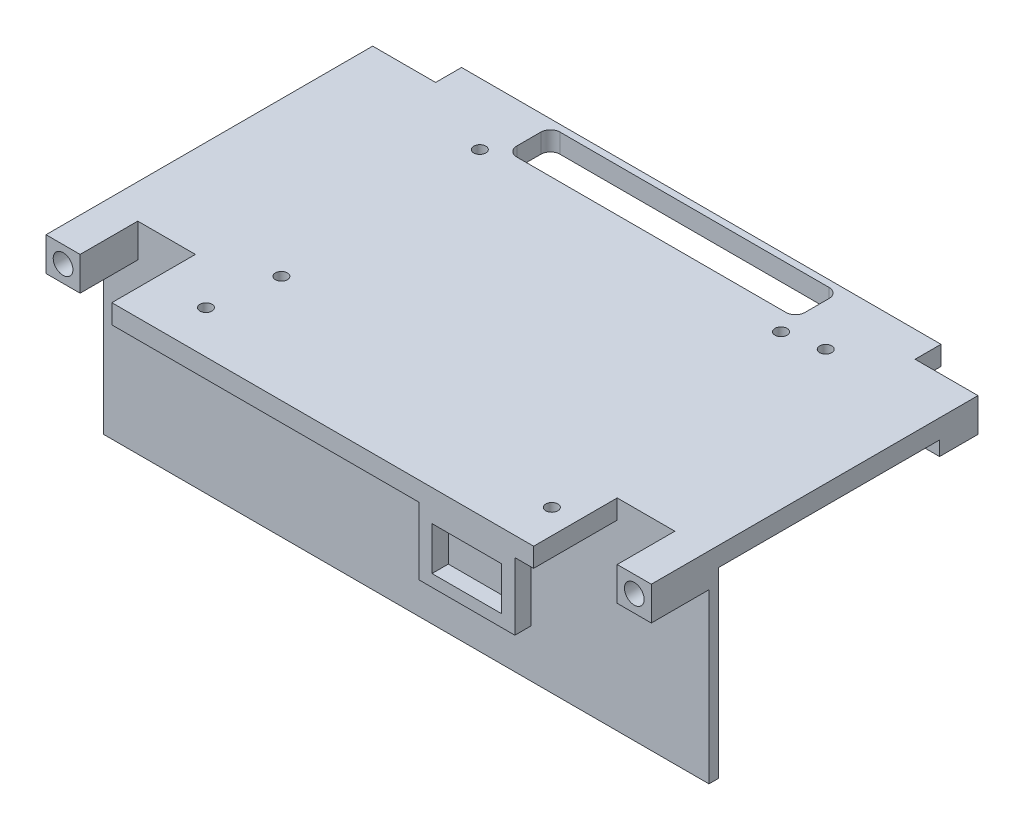
SolidWorks part; units mm, degrees
ref_plane "Front Plane" through (0, 0, 0) normal (0, 0, 1) x (1, 0, 0)
ref_plane "Top Plane" through (0, 0, 0) normal (0, 1, 0) x (1, 0, 0)
ref_plane "Right Plane" through (0, 0, 0) normal (1, 0, 0) x (0, 0, -1)
sketch "Sketch1" plane through (0, 0, 0) normal (0, 1, 0) x (1, 0, 0)
  line L0 (-63, 0) -> (63, 0) construction
  line L1 (-63, -34) -> (-55.9, -34)
  line L2 (-63, -34) -> (-63, 34)
  line L3 (-63, 34) -> (-55.9, 34)
  line L4 (63, -34) -> (63, 34)
  line L5 (-63, -34) -> (63, 34) construction
  line L6 (-63, 34) -> (63, -34) construction
  line L8 (-55.9, 34) -> (-55.9, 41)
  line L9 (-55.9, 41) -> (55.9, 41)
  line L10 (55.9, 34) -> (55.9, 41)
  line L11 (55.9, 34) -> (63, 34)
  line L12 (55.9, -34) -> (55.9, -41)
  line L13 (-55.9, -41) -> (55.9, -41)
  line L14 (-55.9, -34) -> (-55.9, -41)
  line L15 (55.9, -34) -> (63, -34)
  point P0 (0, 0)
  point P10 (0, 41)
  dimension "D1" = 126
  dimension "D2" = 68
  dimension "D3" = 7.1
  dimension "D4" = 7
extrude "Boss-Extrude1" add sketch "Sketch1" along normal blind 4
sketch "Sketch3" plane through (0, 0, 0) normal (0, -1, 0) x (1, 0, 0)
  line L0 (-63, -34) -> (-63, 34) construction
  line L1 (-55.9, -34) -> (-63, -34)
  line L2 (-55.9, -34) -> (-55.9, -26)
  line L3 (-55.9, -26) -> (-63, -26)
  line L4 (-63, -34) -> (-63, -26)
  dimension "D1" = 8
extrude "Boss-Extrude3" add sketch "Sketch3" along normal blind 3
sketch "Sketch4" plane through (0, 0, -34) normal (0, 0, -1) x (-1, 0, 0)
  line L0 (63, -3) -> (55.9, 4) construction
  circle A0 centre (59.45, 0.5) radius 2.05
  dimension "D1" = 4.1
extrude "Cut-Extrude1" cut sketch "Sketch4" against normal blind 7
mirror "Mirror1" about plane through (0, 0, 0) normal (1, 0, 0) of "Cut-Extrude1", "Boss-Extrude3"
mirror "Mirror2" about plane through (0, 0, 0) normal (0, 0, 1) of "Cut-Extrude1", "Boss-Extrude3", "Mirror1"
sketch "Sketch5" plane through (0, 4, 0) normal (0, 1, 0) x (1, 0, 0)
  line L0 (55.9, 41) -> (-55.9, 41) construction
  line L1 (-30, 38) -> (30, 38)
  line L2 (-30, 38) -> (-30, 29)
  line L3 (-30, 29) -> (30, 29)
  line L4 (30, 38) -> (30, 29)
  point P4 (0, 29)
  dimension "D1" = 3
  dimension "D2" = 9
  dimension "D3" = 60
extrude "Cut-Extrude2" cut sketch "Sketch5" against normal through all
sketch "Sketch6" plane through (0, 4, 0) normal (0, 1, 0) x (1, 0, 0)
  line L1 (-38.5, -28) -> (38.5, -28) construction
  line L2 (-38.5, -28) -> (-38.5, 24) construction
  line L3 (-38.5, 24) -> (38.5, 24) construction
  line L4 (38.5, -28) -> (38.5, 24) construction
  line L5 (-38.5, -28) -> (38.5, 24) construction
  line L6 (-38.5, 24) -> (38.5, -28) construction
  circle A0 centre (-38.5, 24) radius 1.25
  circle A1 centre (38.5, 24) radius 1.25
  circle A2 centre (38.5, -28) radius 1.25
  circle A3 centre (-38.5, -28) radius 1.25
  point P0 (0, -2)
  point P9 (0, -2)
  dimension "D4" = 2.5
  dimension "D1" = 77
  dimension "D2" = 52
  dimension "D3" = 2
fillet "Fillet1" radius 2 4 edges at (-30, 2, -38) (-30, 2, -29) (30, 2, -38) (30, 2, -29)
sketch "Sketch7" plane through (0, 4, 0) normal (0, 1, 0) x (1, 0, 0)
  line L0 (55.9, 34) -> (55.9, 41) construction
  line L1 (-55.9, 41) -> (55.9, 41)
  line L2 (-55.9, 41) -> (-55.9, 40)
  line L3 (-55.9, 40) -> (55.9, 40)
  line L4 (55.9, 41) -> (55.9, 40)
  line L5 (-55.9, -34) -> (-55.9, -41) construction
  line L6 (55.9, -41) -> (-55.9, -41)
  line L7 (55.9, -41) -> (55.9, -40)
  line L8 (55.9, -40) -> (-55.9, -40)
  line L9 (-55.9, -41) -> (-55.9, -40)
  dimension "D1" = 1
  dimension "D2" = 1
extrude "Cut-Extrude3" cut sketch "Sketch7" against normal through all
sketch "Sketch8" plane through (0, 0, 0) normal (0, -1, 0) x (1, 0, 0)
  line L0 (63, 26) -> (63, -26) construction
  line L1 (63, 22) -> (-63, 22)
  line L2 (63, 22) -> (63, 20)
  line L3 (63, 20) -> (-63, 20)
  line L4 (-63, 22) -> (-63, 20)
  line L5 (-63, -26) -> (-63, 26) construction
  line L7 (55.9, 40) -> (-55.9, 40) construction
  dimension "D1" = 20
  dimension "D2" = 2
extrude "Boss-Extrude4" add sketch "Sketch8" along normal blind 38
sketch "Sketch9" plane through (0, 4, 0) normal (0, 1, 0) x (1, 0, 0)
  line L0 (63, -22) -> (-63, -22) construction
  line L1 (-55.9, -40) -> (-43.9, -40)
  line L2 (-55.9, -40) -> (-55.9, -22)
  line L3 (-55.9, -22) -> (-43.9, -22)
  line L4 (-43.9, -40) -> (-43.9, -22)
  dimension "D1" = 12
extrude "Cut-Extrude4" cut sketch "Sketch9" against normal blind 10
sketch "Sketch10" plane through (0, -3, 0) normal (0, -1, 0) x (1, 0, 0)
  line L1 (-63, 26) -> (-55.9, 26)
  line L2 (-63, 26) -> (-63, 22)
  line L3 (-63, 22) -> (-55.9, 22)
  line L4 (-55.9, 26) -> (-55.9, 22)
  line L5 (55.9, 26) -> (63, 26)
  line L6 (55.9, 26) -> (55.9, 22)
  line L7 (55.9, 22) -> (63, 22)
  line L8 (63, 26) -> (63, 22)
extrude "Boss-Extrude5" add sketch "Sketch10" against normal up to surface (3 mm away) up to face at (29.4143, 0, 30)
ref_plane "Plane2" through (-56, 0, 0) normal (-1, 0, 0) x (0, 0, 1)
sketch "Sketch12" plane through (-56, 0, 0) normal (-1, 0, 0) x (0, 0, 1)
  line L0 (22, -5.8) -> (22, -16.2)
  line L1 (22, -38) -> (22, -3) construction
  line L2 (22, -16.2) -> (24.7, -13.5)
  line L3 (24.7, -13.5) -> (24.7, -8.5)
  line L4 (24.7, -8.5) -> (22, -5.8)
  line L5 (24.7, -11) -> (22, -11) construction
  line L6 (22, -3) -> (34, -3) construction
  line L7 (24.1, -9) -> (22.6, -9)
  line L8 (24.1, -9) -> (24.1, -13)
  line L9 (24.1, -13) -> (22.6, -13)
  line L10 (22.6, -9) -> (22.6, -13)
  line L11 (22, -20.8) -> (22, -31.2)
  line L12 (22, -31.2) -> (24.7, -28.5)
  line L13 (24.7, -28.5) -> (24.7, -23.5)
  line L14 (24.7, -23.5) -> (22, -20.8)
  line L15 (24.1, -24) -> (22.6, -24)
  line L16 (24.1, -24) -> (24.1, -28)
  line L17 (24.1, -28) -> (22.6, -28)
  line L18 (22.6, -24) -> (22.6, -28)
  line L19 (24.7, -26) -> (22, -26) construction
  point P13 (23.35, -11)
  point P14 (24.1, -11)
  dimension "D1" = 1.5
  dimension "D2" = 0.6
  dimension "D3" = 0.6
  dimension "D4" = 4
  dimension "D5" = 45
  dimension "D6" = 5
  dimension "D7" = 8
  dimension "D8" = 2
extrude "Boss-Extrude6" add sketch "Sketch12" against normal blind 2
ref_plane "Plane3" through (-49.9, 0, 0) normal (1, 0, 0) x (0, 0, -1)
mirror "Mirror3" about plane through (-49.9, 0, 0) normal (1, 0, 0) of "Boss-Extrude6"
sketch "Sketch13" plane through (0, 0, 0) normal (0, -1, 0) x (1, 0, 0)
  line L0 (-28, -29) -> (28, -29) construction
  line L1 (-20, -19.5) -> (20, -19.5)
  line L2 (-20, -19.5) -> (-20, -21.5)
  line L3 (-20, -21.5) -> (20, -21.5)
  line L4 (20, -19.5) -> (20, -21.5)
  point P4 (0, -21.5)
  dimension "D1" = 40
  dimension "D2" = 2
  dimension "D3" = 7.5
extrude "Boss-Extrude7" add sketch "Sketch13" along normal up to surface (38 mm away) up to face at (0, -38, 21)
sketch "Sketch14" plane through (0, 0, 0) normal (1, 0, 0) x (0, 0, -1)
  line L0 (-20, -19) -> (19.5, -19) construction
  line L1 (-20, -38) -> (-20, 0) construction
  line L2 (19.5, -38) -> (19.5, 0) construction
  line L3 (-0.25, -38) -> (-0.25, 0) construction
  line L4 (-20, 0) -> (26, 0) construction
  line L5 (-22, -31.2) -> (-24.7, -28.5) construction
  line L6 (-24.1, -24) -> (-22.6, -24) construction
  line L7 (-24.1, -28) -> (-24.1, -24) construction
  line L8 (-22.6, -28) -> (-24.1, -28) construction
  line L9 (-22.6, -24) -> (-22.6, -28) construction
  line L10 (-22, -20.8) -> (-22, -31.2) construction
  line L11 (-24.7, -23.5) -> (-22, -20.8) construction
  line L12 (-24.7, -28.5) -> (-24.7, -23.5) construction
  line L13 (-24.1, -13) -> (-24.1, -9) construction
  line L14 (-24.1, -9) -> (-22.6, -9) construction
  line L15 (-22.6, -9) -> (-22.6, -13) construction
  line L16 (-22.6, -13) -> (-24.1, -13) construction
  line L17 (-22, -5.8) -> (-22, -16.2) construction
  line L18 (-22, -16.2) -> (-24.7, -13.5) construction
  line L19 (-24.7, -13.5) -> (-24.7, -8.5) construction
  line L20 (-24.7, -8.5) -> (-22, -5.8) construction
  line L21 (-22, -31.2) -> (-24.7, -28.5) construction
  line L22 (-24.1, -24) -> (-22.6, -24) construction
  line L23 (-24.1, -28) -> (-24.1, -24) construction
  line L24 (-22.6, -28) -> (-24.1, -28) construction
  line L25 (-22.6, -24) -> (-22.6, -28) construction
  line L26 (-22, -20.8) -> (-22, -31.2) construction
  line L27 (-24.7, -23.5) -> (-22, -20.8) construction
  line L28 (-24.7, -28.5) -> (-24.7, -23.5) construction
  line L29 (-24.1, -13) -> (-24.1, -9) construction
  line L30 (-24.1, -9) -> (-22.6, -9) construction
  line L31 (-22.6, -9) -> (-22.6, -13) construction
  line L32 (-22.6, -13) -> (-24.1, -13) construction
  line L33 (-22, -5.8) -> (-22, -16.2) construction
  line L34 (-22, -16.2) -> (-24.7, -13.5) construction
  line L35 (-24.7, -13.5) -> (-24.7, -8.5) construction
  line L36 (-24.7, -8.5) -> (-22, -5.8) construction
  line L37 (24.2, -8.5) -> (21.5, -5.8)
  line L38 (24.2, -13.5) -> (24.2, -8.5)
  line L39 (21.5, -16.2) -> (24.2, -13.5)
  line L40 (21.5, -5.8) -> (21.5, -16.2)
  line L41 (22.1, -13) -> (23.6, -13)
  line L42 (22.1, -9) -> (22.1, -13)
  line L43 (23.6, -9) -> (22.1, -9)
  line L44 (23.6, -13) -> (23.6, -9)
  line L45 (24.2, -28.5) -> (24.2, -23.5)
  line L46 (24.2, -23.5) -> (21.5, -20.8)
  line L47 (21.5, -20.8) -> (21.5, -31.2)
  line L48 (22.1, -24) -> (22.1, -28)
  line L49 (22.1, -28) -> (23.6, -28)
  line L50 (23.6, -28) -> (23.6, -24)
  line L51 (23.6, -24) -> (22.1, -24)
  line L52 (21.5, -31.2) -> (24.2, -28.5)
  point P11 (-0.25, -19)
extrude "Boss-Extrude8" add sketch "Sketch14" along normal mid plane 2
sketch "Sketch15" plane through (0, 0, 0) normal (1, 0, 0) x (0, 0, -1)
  line L0 (19.5, 0) -> (19.5, -5)
  line L1 (19.5, -38) -> (19.5, 0) construction
  line L2 (19.5, -5) -> (16.6132, 0)
  line L3 (-20, 0) -> (26, 0) construction
  line L4 (16.6132, 0) -> (19.5, 0)
  dimension "D1" = 60
  dimension "D2" = 5
extrude "Boss-Extrude9" add sketch "Sketch15" against normal up to surface and the other way up to surface up to face at (-20, -19, -20.5) other way up to face at (20, -19, -20.5)
sketch "Sketch16" plane through (0, 0, 40) normal (0, 0, 1) x (1, 0, 0)
  line L0 (40, 0) -> (20, -14) construction
  line L1 (40, 0) -> (20, 0)
  line L2 (40, 0) -> (40, -14)
  line L3 (40, -14) -> (20, -14)
  line L4 (20, 0) -> (20, -14)
  line L5 (55.9, 0) -> (-43.9, 0) construction
  line L6 (22.75, -2.5) -> (37.25, -2.5)
  line L7 (22.75, -2.5) -> (22.75, -11.5)
  line L8 (22.75, -11.5) -> (37.25, -11.5)
  line L9 (37.25, -2.5) -> (37.25, -11.5)
  line L10 (22.75, -2.5) -> (37.25, -11.5) construction
  line L11 (22.75, -11.5) -> (37.25, -2.5) construction
  line L12 (63, -38) -> (63, -3) construction
  point P5 (30, -7)
  dimension "D1" = 20
  dimension "D2" = 14
  dimension "D3" = 14.5
  dimension "D4" = 9
  dimension "D5" = 23
extrude "Boss-Extrude10" add sketch "Sketch16" against normal blind 4
sketch "Sketch17" plane through (0, 0, 0) normal (0, -1, 0) x (1, 0, 0)
  line L6 (-43.9, 22) -> (-55.9, 22) construction
  line L7 (55.9, 40) -> (43.9, 40)
  line L8 (55.9, 40) -> (55.9, 22)
  line L9 (55.9, 22) -> (43.9, 22)
  line L10 (43.9, 40) -> (43.9, 22)
  line L13 (-43.9, 40) -> (-43.9, 22) construction
extrude "Cut-Extrude5" cut sketch "Sketch17" against normal through all
sketch "Sketch18" plane through (0, 4, 0) normal (0, 1, 0) x (1, 0, 0)
  line L5 (-55.9, 40) -> (55.9, 40) construction
  line L6 (55.9, 34) -> (49.9, 34)
  line L7 (55.9, 34) -> (55.9, 40)
  line L8 (55.9, 40) -> (49.9, 40)
  line L9 (49.9, 34) -> (49.9, 40)
  line L11 (-55.9, 34) -> (-49.9, 34)
  line L12 (-55.9, 34) -> (-55.9, 40)
  line L13 (-55.9, 40) -> (-49.9, 40)
  line L14 (-49.9, 34) -> (-49.9, 40)
extrude "Cut-Extrude6" cut sketch "Sketch18" against normal through all
sketch "Sketch20" plane through (0, 4, 0) normal (0, 1, 0) x (1, 0, 0)
  line L0 (-31, 25) -> (31, -17) construction
  line L1 (-31, 25) -> (31, 25) construction
  line L2 (-31, 25) -> (-31, -17) construction
  line L3 (-31, -17) -> (31, -17) construction
  line L4 (31, 25) -> (31, -17) construction
  line L5 (-38.5, 26) -> (38.5, 26) construction
  line L6 (-38.5, 26) -> (-38.5, -26) construction
  line L7 (-38.5, -26) -> (38.5, -26) construction
  line L8 (38.5, 26) -> (38.5, -26) construction
  line L11 (38.5, 26) -> (-38.5, -26) construction
  circle A0 centre (-31, 25) radius 3 construction
  circle A1 centre (-31, -17) radius 3 construction
  circle A2 centre (31, -17) radius 3 construction
  circle A3 centre (31, 25) radius 3 construction
  circle A4 centre (-38.5, 26) radius 3 construction
  circle A5 centre (38.5, 26) radius 3 construction
  circle A6 centre (38.5, -26) radius 3 construction
  circle A7 centre (-38.5, -26) radius 3 construction
  point P18 (0, 4)
  dimension "D3" = 6
  dimension "D1" = 42
  dimension "D2" = 62
  dimension "D4" = 4
  dimension "D6" = 77
  dimension "D7" = 52
sketch "Sketch22" plane through (0, 4, 0) normal (0, 1, 0) x (1, 0, 0)
  circle A0 centre (-31, 25) radius 1.25 construction
  circle A1 centre (31, 25) radius 1.25
  circle A2 centre (31, -17) radius 1.25 construction
  circle A3 centre (-31, -17) radius 1.25
  dimension "D1" = 2.5
extrude "Cut-Extrude7" cut sketch "Sketch22" against normal up to surface (4 mm away) up to face at (15, 0, 34.5)
sketch "Sketch25" plane through (0, 0, -21.5) normal (0, 0, -1) x (-1, 0, 0)
  line L0 (63, -38) -> (-63, -38) construction
  line L1 (-20, -38) -> (-14, -38)
  line L2 (-20, -38) -> (-20, 0)
  line L3 (-20, 0) -> (-14, 0)
  line L4 (-14, -38) -> (-14, 0)
  line L5 (-20, -38) -> (-20, 0) construction
  line L6 (20, 0) -> (-20, 0) construction
  line L7 (-20, -38) -> (20, -38) construction
  line L8 (20, 0) -> (14, 0)
  line L9 (20, 0) -> (20, -38)
  line L10 (20, -38) -> (14, -38)
  line L11 (14, 0) -> (14, -38)
  dimension "D1" = 6
extrude "Cut-Extrude11" cut sketch "Sketch25" against normal blind 10
sketch "Sketch26" plane through (-1, 0, 0) normal (-1, 0, 0) x (0, 0, 1)
  line L1 (-21.5, -5.8) -> (-27.2016, -5.8)
  line L2 (-21.5, -5.8) -> (-21.5, -36.3625)
  line L3 (-21.5, -36.3625) -> (-27.2016, -36.3625)
  line L4 (-27.2016, -5.8) -> (-27.2016, -36.3625)
  line L5 (22, -5.8) -> (28.5342, -5.8)
  line L6 (22, -5.8) -> (22, -34.3243)
  line L7 (22, -34.3243) -> (28.5342, -34.3243)
  line L8 (28.5342, -5.8) -> (28.5342, -34.3243)
extrude "Cut-Extrude12" cut sketch "Sketch26" against normal through all both and the other way through all
sketch "Sketch27" plane through (0, 4, 0) normal (0, 1, 0) x (1, 0, 0)
  line L1 (-33.2, -30.5) -> (38.8, -30.5) construction
  line L2 (-33.2, -30.5) -> (-33.2, 26.5) construction
  line L3 (-33.2, 26.5) -> (38.8, 26.5) construction
  line L4 (38.8, -30.5) -> (38.8, 26.5) construction
  line L5 (-33.2, -30.5) -> (38.8, 26.5) construction
  line L6 (-33.2, 26.5) -> (38.8, -30.5) construction
  circle A0 centre (-33.2, 26.5) radius 1.25
  circle A1 centre (-33.2, -30.5) radius 1.25
  circle A2 centre (38.8, -30.5) radius 1.25
  circle A3 centre (38.8, 26.5) radius 1.25
  circle A5 centre (31, 25) radius 1.25 construction
  circle A6 centre (31, 25) radius 1.25 construction
  point P0 (2.8, -2)
  dimension "D1" = 72
  dimension "D2" = 57
  dimension "D3" = 2
  dimension "D4" = 2.8
extrude "Cut-Extrude13" cut sketch "Sketch27" against normal through all
sketch "Sketch28" plane through (0, 4, 0) normal (0, 1, 0) x (1, 0, 0)
  line L0 (49.9, 40) -> (49.9, 34) construction
  line L1 (-49.9, 40) -> (49.9, 40)
  line L2 (-49.9, 40) -> (-49.9, 39.4)
  line L3 (-49.9, 39.4) -> (49.9, 39.4)
  line L4 (49.9, 40) -> (49.9, 39.4)
  line L5 (-43.9, -40) -> (-43.9, -22) construction
  line L6 (43.9, -40) -> (-43.9, -40)
  line L7 (43.9, -40) -> (43.9, -39.4)
  line L8 (43.9, -39.4) -> (-43.9, -39.4)
  line L9 (-43.9, -40) -> (-43.9, -39.4)
  dimension "D1" = 0.6
  dimension "D2" = 0.6
extrude "Cut-Extrude14" cut sketch "Sketch28" against normal through all
